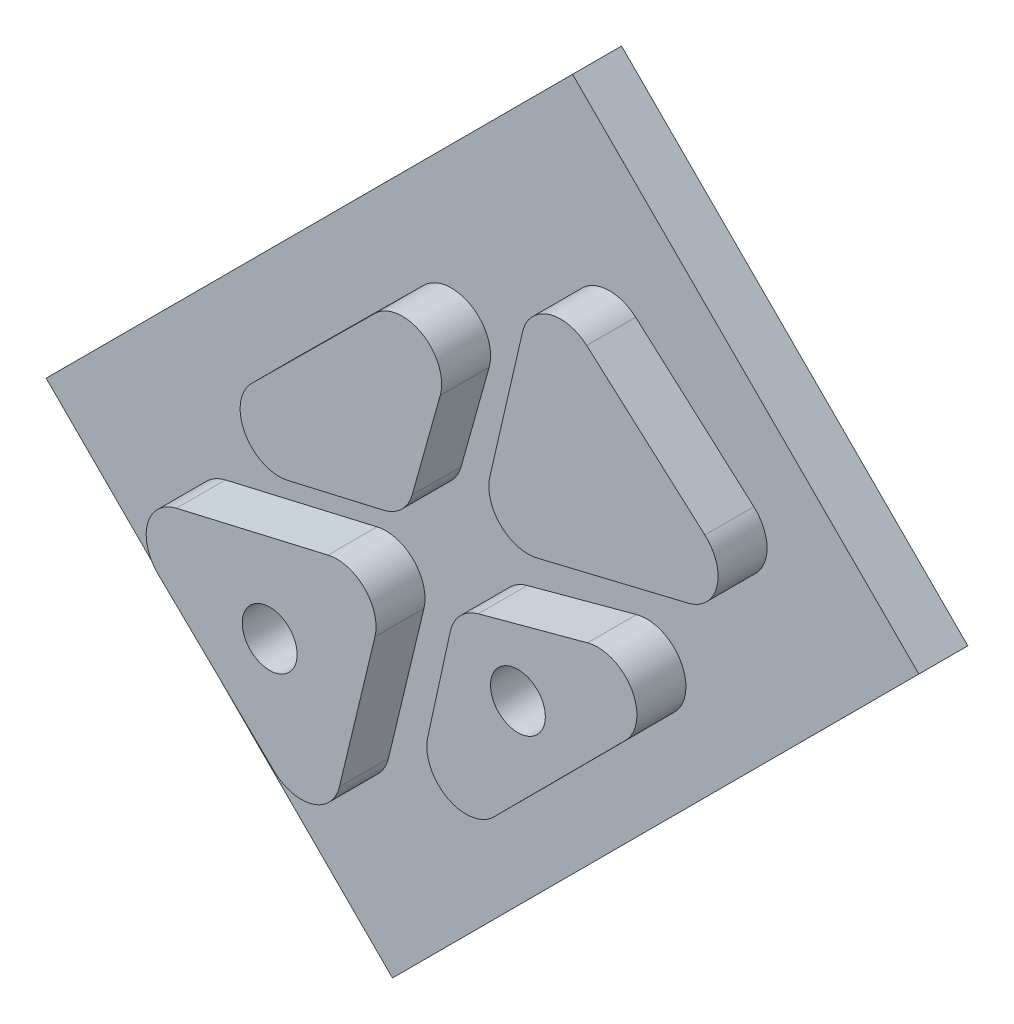
SolidWorks part; units mm, degrees
ref_plane "Front Plane" through (0, 0, 0) normal (0, 0, 1) x (1, 0, 0)
ref_plane "Top Plane" through (0, 0, 0) normal (0, 1, 0) x (1, 0, 0)
ref_plane "Right Plane" through (0, 0, 0) normal (1, 0, 0) x (0, 0, -1)
sketch "Sketch1" plane through (0, 0, 0) normal (0, 0, 1) x (1, 0, 0)
  line L0 (187.2863, -255.5362) -> (255.5362, -187.2863)
  line L1 (255.5362, -187.2863) -> (300.4375, -232.1876)
  line L2 (300.4375, -232.1876) -> (232.1876, -300.4375)
  line L3 (232.1876, -300.4375) -> (187.2863, -255.5362)
extrude "Boss-Extrude1" add sketch "Sketch1" along normal blind 6.35
sketch "Sketch2" plane through (-122.9993, -379.3509, 6.35) normal (0, 0, 1) x (1, 0, 0)
  line L0 (405.6125, 147.9088) -> (409.1976, 148.7741)
  line L1 (380.2445, 174.2375) -> (372.318, 139.8722)
  line L2 (405.6125, 147.9088) -> (372.318, 139.8722)
  line L3 (406.9485, 150.9016) -> (409.1976, 148.7741)
  line L4 (406.9485, 150.9016) -> (380.3231, 174.5573)
  line L5 (380.2445, 174.2375) -> (380.3231, 174.5573)
  line L6 (364.4542, 107.0265) -> (369.6874, 130.9219)
  line L7 (389.9157, 136.3777) -> (369.6874, 130.9219)
  line L8 (369.845, 105.0775) -> (404.5283, 139.8722)
  line L9 (389.9157, 136.3777) -> (404.5283, 139.8722)
  line L10 (364.4542, 107.0265) -> (362.3893, 97.5978)
  line L11 (369.845, 105.0775) -> (362.3893, 97.5978)
  line L12 (353.6319, 99.0231) -> (352.4655, 94.6167)
  line L13 (352.4655, 94.6167) -> (353.6319, 99.0231)
  line L14 (353.6319, 99.0231) -> (361.1873, 130.4316)
  line L15 (358.6524, 129.8431) -> (324.4547, 121.9038)
  line L16 (347.736, 99.3265) -> (352.4655, 94.6167)
  line L17 (347.736, 99.3265) -> (324.4547, 121.9038)
  line L18 (358.6524, 129.8431) -> (361.1873, 130.4316)
  line L19 (341.261, 132.8029) -> (363.2789, 137.8788)
  line L20 (371.0791, 165.747) -> (363.2789, 137.8788)
  line L21 (365.3803, 164.8104) -> (330.49, 130.2308)
  line L22 (330.49, 130.2308) -> (341.261, 132.8029)
  line L23 (365.3803, 164.8104) -> (373.0557, 172.4174)
  line L24 (371.0791, 165.747) -> (373.0557, 172.4174)
extrude "Boss-Extrude2" add sketch "Sketch2" along normal blind 6.35 contours L18 L15 L17 L16 L12 L14 | L11 L8 L9 L7 L6 L10 | L5 L1 L2 L0 L3 L4 | L20 L24 L23 L21 L22 L19
fillet "Fillet1" radius 5.08 12 edges at (250.0564, -206.9335, 9.525) (257.3238, -204.7936, 9.525) (286.1983, -230.5768, 9.525) (249.3187, -239.4787, 9.525) (239.39, -281.7531, 9.525) (246.6881, -248.429, 9.525) (281.529, -239.4787, 9.525) (201.4555, -257.4471, 9.525) (238.1881, -248.9193, 9.525) (207.4907, -249.1201, 9.525) (240.2797, -241.4721, 9.525) (229.4662, -284.7342, 9.525)
sketch "Sketch3" plane through (0, 0, 12.7) normal (0, 0, 1) x (1, 0, 0)
  circle A0 centre (254.8027, -254.8539) radius 3.556
  circle A1 centre (222.6161, -263.9547) radius 3.556
  dimension "D1" = 7.112
  dimension "D2" = 7.112
extrude "Cut-Extrude1" cut sketch "Sketch3" against normal through all and the other way through all
